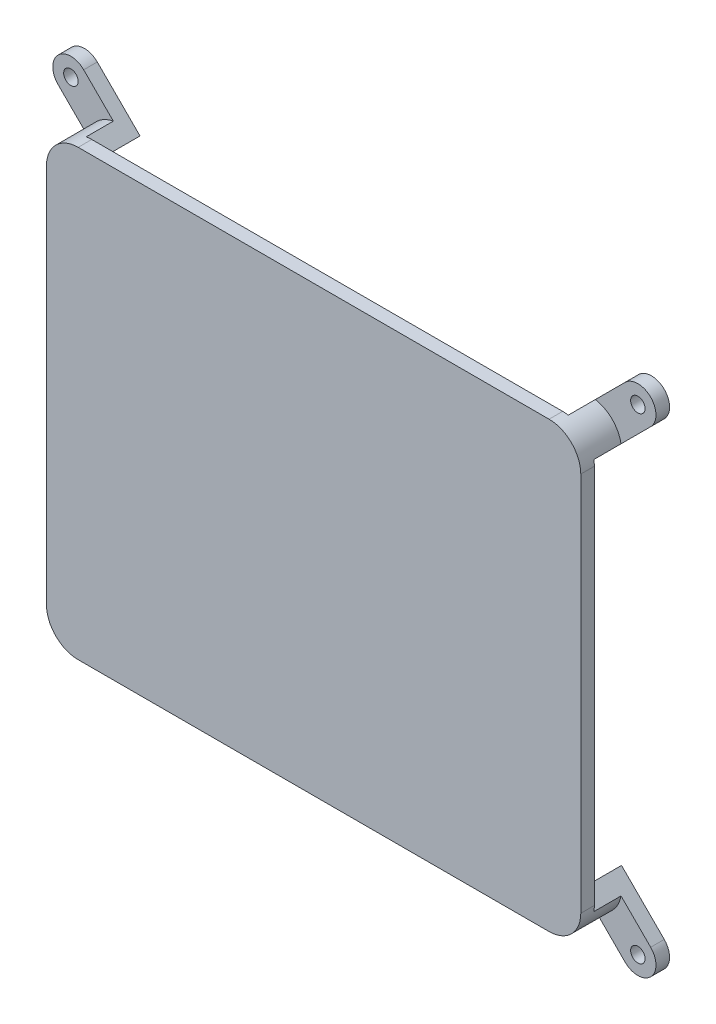
SolidWorks part; units mm, degrees
ref_plane "Front Plane" through (0, 0, 0) normal (0, 0, 1) x (1, 0, 0)
ref_plane "Top Plane" through (0, 0, 0) normal (0, 1, 0) x (1, 0, 0)
ref_plane "Right Plane" through (0, 0, 0) normal (1, 0, 0) x (0, 0, -1)
sketch "Sketch1" plane through (0, 0, 0) normal (0, 0, 1) x (1, 0, 0)
  line L4 (-72.1221, 155) -> (-72.1221, 71) construction
  line L5 (-64.1221, 63) -> (39.8779, 63) construction
  line L6 (39.8779, 163) -> (-64.1221, 163) construction
  line L7 (47.8779, 71) -> (47.8779, 155) construction
  line L8 (-71.1221, 155) -> (-71.1221, 71)
  line L9 (-64.1221, 64) -> (39.8779, 64)
  line L10 (46.8779, 71) -> (46.8779, 155)
  line L11 (39.8779, 162) -> (-64.1221, 162)
  arc A4 (-64.1221, 163) -> (-72.1221, 155) centre (-64.1221, 155) ccw construction
  arc A5 (-72.1221, 71) -> (-64.1221, 63) centre (-64.1221, 71) ccw construction
  arc A6 (39.8779, 63) -> (47.8779, 71) centre (39.8779, 71) ccw construction
  arc A7 (47.8779, 155) -> (39.8779, 163) centre (39.8779, 155) ccw construction
  arc A8 (-71.1221, 71) -> (-64.1221, 64) centre (-64.1221, 71) ccw
  arc A9 (39.8779, 64) -> (46.8779, 71) centre (39.8779, 71) ccw
  arc A10 (46.8779, 155) -> (39.8779, 162) centre (39.8779, 155) ccw
  arc A11 (-64.1221, 162) -> (-71.1221, 155) centre (-64.1221, 155) ccw
  dimension "D1" = 1
extrude "Boss-Extrude1" add sketch "Sketch1" against normal blind 3
sketch "Sketch2" plane through (0, 0, -3) normal (0, 0, -1) x (-1, 0, 0)
  line L0 (-46.7684, 156.2336) -> (-43.8779, 153.3431)
  line L1 (-42.7064, 157.8284) -> (-50.4845, 165.6066) construction
  line L3 (-41.1115, 161.8904) -> (-38.2211, 159)
  line L5 (-39.8779, 159) -> (-38.2211, 159)
  line L6 (-43.8779, 155) -> (-43.8779, 153.3431)
  arc A0 (-39.8779, 162) -> (-46.8779, 155) centre (-39.8779, 155) ccw construction
  arc A1 (-41.1115, 161.8904) -> (-46.7684, 156.2336) centre (-39.8779, 155) ccw
  arc A2 (-39.8779, 159) -> (-43.8779, 155) centre (-39.8779, 155) ccw
  arc A5 (-39.8779, 162) -> (-46.8779, 155) centre (-39.8779, 155) ccw construction
  dimension "D1" = 3
extrude "Boss-Extrude2" add sketch "Sketch2" along normal up to surface (6 mm away)
sketch "Sketch3" plane through (0, 0, -9) normal (0, 0, -1) x (-1, 0, 0)
  line L4 (-43.8779, 153.3431) -> (-43.8779, 155)
  line L5 (-39.8779, 159) -> (-38.2211, 159)
  line L6 (-38.2211, 159) -> (-41.1115, 161.8904)
  line L7 (-46.7684, 156.2336) -> (-43.8779, 153.3431)
  line L8 (-43.8779, 153.3431) -> (-43.8779, 155)
  line L9 (-39.8779, 159) -> (-38.2211, 159)
  line L10 (-38.2211, 159) -> (-47.6561, 168.435)
  line L11 (-53.313, 162.7782) -> (-43.8779, 153.3431)
  circle A0 centre (-50.4845, 165.6066) radius 1.6
  circle A1 centre (-50.4845, 165.6066) radius 4
  arc A2 (-39.8779, 159) -> (-43.8779, 155) centre (-39.8779, 155) ccw
  arc A3 (-41.1115, 161.8904) -> (-46.7684, 156.2336) centre (-39.8779, 155) ccw
  arc A4 (-39.8779, 159) -> (-43.8779, 155) centre (-39.8779, 155) ccw
  arc A6 (-47.6561, 168.435) -> (-53.313, 162.7782) centre (-50.4845, 165.6066) ccw
  dimension "D1" = 0
  dimension "D2" = 0
extrude "Boss-Extrude3" add sketch "Sketch3" along normal blind 3
ref_plane "Plane1" through (0, 113, 0) normal (0, 1, 0) x (1, 0, 0)
ref_plane "Plane2" through (-12.1221, 0, 0) normal (-1, 0, 0) x (0, 0, 1)
mirror "Mirror1" about plane through (-12.1221, 0, 0) normal (-1, 0, 0) of "Boss-Extrude2", "Boss-Extrude3"
mirror "Mirror2" about plane through (0, 113, 0) normal (0, 1, 0) of "Mirror1", "Boss-Extrude2", "Boss-Extrude3"
